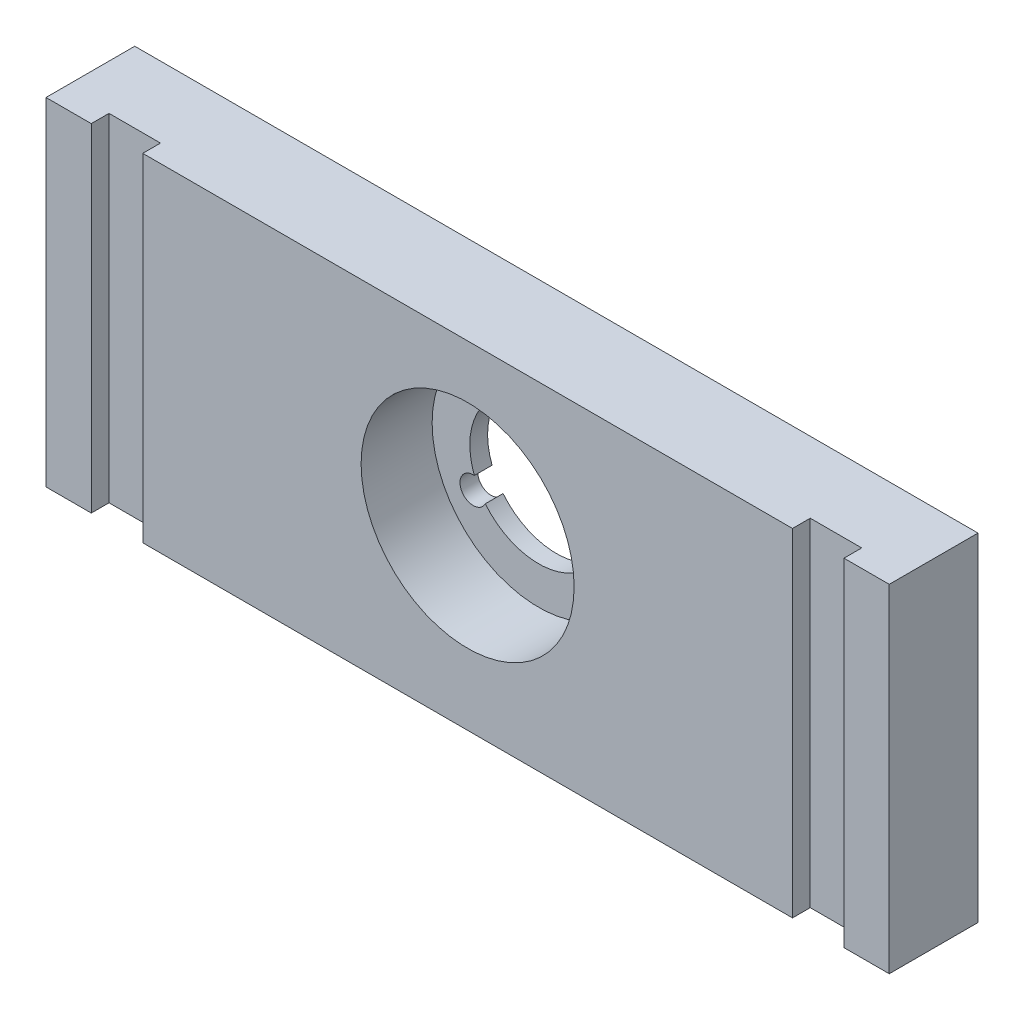
SolidWorks part; units mm, degrees
ref_plane "Plan de face" through (0, 0, 0) normal (0, 0, 1) x (1, 0, 0)
ref_plane "Plan de dessus" through (0, 0, 0) normal (0, 1, 0) x (1, 0, 0)
ref_plane "Plan de droite" through (0, 0, 0) normal (1, 0, 0) x (0, 0, -1)
sketch "Esquisse1" plane through (0, 0, 0) normal (0, 0, 1) x (1, 0, 0)
  line L0 (0, 0) -> (95, 0)
  line L1 (95, 0) -> (95, -38)
  line L2 (95, -38) -> (0, -38)
  line L3 (0, -38) -> (0, 0)
  line L4 (0, 0) -> (95, -36) construction
  line L5 (47.5, -18) -> (47.5, 0) construction
  line L6 (47.5, -18) -> (0, -18) construction
  arc A0 (46.2636, -10.3493) -> (40.2561, -20.7546) centre (47.5, -18) ccw
  arc A1 (48.7364, -10.3493) -> (46.2636, -10.3493) centre (47.5, -9.5) ccw
  arc A2 (53.5075, -22.8961) -> (54.7439, -20.7546) centre (54.8612, -22.25) ccw
  arc A3 (40.2561, -20.7546) -> (41.4925, -22.8961) centre (40.1388, -22.25) ccw
  arc A4 (54.7439, -20.7546) -> (48.7364, -10.3493) centre (47.5, -18) ccw
  arc A5 (41.4925, -22.8961) -> (53.5075, -22.8961) centre (47.5, -18) ccw
  point P0 (0, 0)
  dimension "D1" = 38
  dimension "D5" = 7.75
  dimension "D6" = 1.5
  dimension "D2" = 95
  dimension "D3" = 47.5
  dimension "D4" = 18
  dimension "D7" = 8.5
  dimension "D8" = 8.5
  dimension "D9" = 8.5
extrude "Extrusion1" add sketch "Esquisse1" along normal blind 10
sketch "Esquisse3" plane through (0, 0, 10) normal (0, 0, 1) x (1, 0, 0)
  circle A0 centre (47.5, -18) radius 12
  dimension "D1" = 24
extrude "Extrusion3" cut sketch "Esquisse3" against normal blind 8
sketch "Esquisse4" plane through (0, 0, 10) normal (0, 0, 1) x (1, 0, 0)
  line L0 (5.1, 0) -> (10.9, 0)
  line L1 (0, 0) -> (0, -38) construction
  line L2 (5.1, -38) -> (5.1, 0)
  line L3 (95, 0) -> (0, 0) construction
  line L4 (10.9, -38) -> (10.9, 0)
  line L5 (10.9, -38) -> (5.1, -38)
  line L6 (0, -38) -> (95, -38) construction
  line L7 (47.5, -18) -> (47.5, 3.4527) construction
  line L8 (84.1, -38) -> (89.9, -38)
  line L9 (84.1, -38) -> (84.1, 0)
  line L10 (89.9, -38) -> (89.9, 0)
  line L11 (89.9, 0) -> (84.1, 0)
  dimension "D1" = 5.8
  dimension "D2" = 5.1
extrude "Extrusion4" cut sketch "Esquisse4" against normal blind 2
